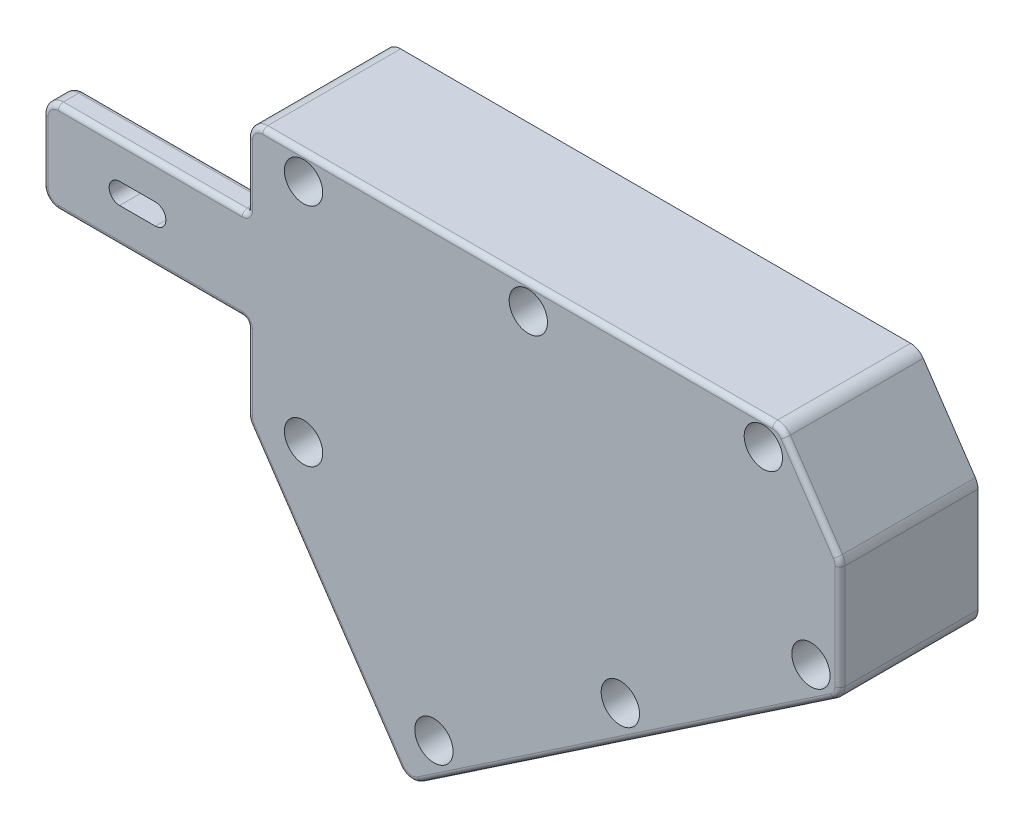
SolidWorks part; units mm, degrees
ref_plane "Front Plane" through (0, 0, 0) normal (0, 0, 1) x (1, 0, 0)
ref_plane "Top Plane" through (0, 0, 0) normal (0, 1, 0) x (1, 0, 0)
ref_plane "Right Plane" through (0, 0, 0) normal (1, 0, 0) x (0, 0, -1)
sketch "Sketch4" plane through (0, 0, -1794.9976) normal (0, 0, 1) x (1, 0, 0)
  line L0 (0.0099, 24.9921) -> (104.4079, 24.9921)
  line L1 (104.4079, 24.9921) -> (116.0099, 7.7914)
  line L2 (116.0099, 7.7914) -> (116.0099, -15.1718)
  line L3 (116.0099, -15.1718) -> (31.3812, -72.2546)
  line L4 (31.3812, -72.2546) -> (0.0099, -25.7448)
  line L5 (0.0099, -25.7448) -> (0.0099, 24.9921)
  circle A0 centre (11.0099, 20) radius 2.25
  circle A1 centre (55, 20) radius 2.25
  circle A2 centre (101.0003, 20.0004) radius 2.25
  circle A3 centre (110.313, -12.2324) radius 2.25
  circle A4 centre (73.0063, -37.396) radius 2.25
  circle A5 centre (36.5275, -62.0013) radius 2.25
  circle A6 centre (11.0099, -24.17) radius 2.25
  dimension "D1" = 4.5
extrude "Boss-Extrude1" add sketch "Sketch4" along normal blind 25
sketch "Sketch5" plane through (0.0099, 0, 0) normal (-1, 0, 0) x (0, 0, 1)
  line L0 (-1794.9976, -111910.8353) -> (-1794.9976, 111863.5728) construction
  circle A0 centre (-1794.9976, 0) radius 15.875
extrude "Cut-Extrude1" cut sketch "Sketch5" against normal up to surface (30 mm away)
sketch "Sketch6" plane through (-11.9282, -8.0457, 0) normal (-0.829, -0.5592, 0) x (0, 0, 1)
  circle A0 centre (-1794.9976, -50.3274) radius 15.875
extrude "Cut-Extrude2" cut sketch "Sketch6" against normal up to surface (35 mm away)
sketch "Sketch7" plane through (30.0099, 0, 0) normal (-1, 0, 0) x (0, 0, 1)
  line L0 (-1794.9976, -111910.8353) -> (-1794.9976, 111863.5728) construction
  circle A0 centre (-1794.9976, 0) radius 14.75
extrude "Cut-Extrude3" cut sketch "Sketch7" against normal blind 3
sketch "Sketch8" plane through (17.0881, 11.5261, 0) normal (-0.829, -0.5592, 0) x (0, 0, 1)
  circle A0 centre (-1794.9976, -50.3274) radius 14.75
extrude "Cut-Extrude4" cut sketch "Sketch8" against normal blind 3
sketch "Sketch9" plane through (0, 0, -1794.9976) normal (0, 0, -1) x (-1, 0, 0)
  line L7 (-33, 15.5) -> (-85.2612, 15.5)
  line L8 (-85.2612, 15.5) -> (-94.5944, 21.7954)
  line L9 (-94.5944, 21.7954) -> (-111.932, -3.903)
  line L10 (-111.932, -3.903) -> (-56.384, -41.3707)
  line L11 (-56.384, -41.3707) -> (-38.934, -15.5)
  line L12 (-38.934, -15.5) -> (-33, -15.5)
  line L13 (-33, -15.5) -> (-33, 15.5)
  line L14 (-33, 15.5) -> (-85.2612, 15.5)
  line L15 (-85.2612, 15.5) -> (-94.5944, 21.7954)
  line L16 (-94.5944, 21.7954) -> (-111.932, -3.903)
  line L17 (-111.932, -3.903) -> (-56.384, -41.3707)
  line L18 (-56.384, -41.3707) -> (-38.934, -15.5)
  line L19 (-38.934, -15.5) -> (-33, -15.5)
  line L20 (-33, -15.5) -> (-33, 15.5)
  dimension "D1" = 0
extrude "Cut-Extrude5" cut sketch "Sketch9" against normal blind 16
sketch "Sketch10" plane through (0, 0, -1778.9976) normal (0, 0, -1) x (-1, 0, 0)
  line L0 (-165897.5145, 111838.5807) -> (165830.1531, -111914.5563) construction
  line L1 (-200090, -0.0079) -> (200022.6386, -0.0079) construction
  circle A0 centre (-89.9882, -0.0079) radius 15.05
extrude "Cut-Extrude6" cut sketch "Sketch10" against normal blind 4
sketch "Sketch11" plane through (0, 0, -1769.9976) normal (0, 0, 1) x (1, 0, 0)
  line L0 (0.0099, 9) -> (-39.9901, 9)
  line L1 (0.0099, 200024.9921) -> (0.0099, -200075.9756) construction
  line L2 (-39.9901, 9) -> (-39.9901, -9)
  line L3 (-39.9901, -9) -> (0.0099, -9)
  line L4 (0.0099, -9) -> (0.0099, 9)
  dimension "D1" = 40
  dimension "D2" = 18
  dimension "D3" = 9
extrude "Boss-Extrude2" add sketch "Sketch11" against normal blind 5
sketch "Sketch12" plane through (0, 0, -1769.9976) normal (0, 0, 1) x (1, 0, 0)
  line L0 (-17.9901, -2.0579) -> (-24.9901, -2.0579) construction
  line L1 (-24.9901, 2.0421) -> (-17.9901, 2.0421) construction
  line L2 (-17.9901, -2.0579) -> (-24.9901, -2.0579)
  line L3 (-24.9901, 2.0421) -> (-17.9901, 2.0421)
  arc A0 (-24.9901, 2.0421) -> (-24.9901, -2.0579) centre (-24.9901, -0.0079) ccw construction
  arc A1 (-17.9901, -2.0579) -> (-17.9901, 2.0421) centre (-17.9901, -0.0079) ccw construction
  arc A2 (-24.9901, 2.0421) -> (-24.9901, -2.0579) centre (-24.9901, -0.0079) ccw
  arc A3 (-17.9901, -2.0579) -> (-17.9901, 2.0421) centre (-17.9901, -0.0079) ccw
extrude "Cut-Extrude7" cut sketch "Sketch12" against normal up to next
fillet "Fillet4" radius 3 6 edges at (31.3812, -72.2546, -1782.4976) (0.0099, -25.7448, -1782.4976) (0.0099, 24.9921, -1782.4976) (104.4079, 24.9921, -1782.4976) (116.0099, 7.7914, -1782.4976) (116.0099, -15.1718, -1782.4976)
fillet "Fillet5" radius 3 2 edges at (-39.9901, 9, -1772.4976) (-39.9901, -9, -1772.4976)
sketch "Sketch14" plane through (0, 0, -1769.9976) normal (0, 0, 1) x (1, 0, 0)
  circle A0 centre (110.313, -12.2324) radius 3.75
  circle A1 centre (73.0063, -37.396) radius 3.75
  circle A2 centre (36.5275, -62.0013) radius 3.75
  circle A3 centre (11.0099, -24.17) radius 3.75
  circle A4 centre (11.0099, 20) radius 3.75
  circle A5 centre (55, 20) radius 3.75
  circle A6 centre (101.0003, 20.0004) radius 3.75
  dimension "D1" = 7.5
extrude "Cut-Extrude8" cut sketch "Sketch14" against normal blind 7.5
fillet "Fillet7" radius 1 8 edges at (0.0099, -9, -1772.4976) (0.0099, 0, -1774.9976) (0.0099, 9, -1772.4976) (-18.4901, 9, -1774.9976) (-39.1114, 8.1213, -1774.9976) (-39.9901, 0, -1774.9976) (-39.1114, -8.1213, -1774.9976) (-18.4901, -9, -1774.9976)
sketch "Sketch15" plane through (0, 0, -1794.9976) normal (0, 0, -1) x (-1, 0, 0)
  line L14 (-8.9953, -35.4896) -> (-7.3373, -36.608)
  line L15 (-2.0099, -15.875) -> (-2.0099, -24.8276)
  line L16 (-2.1809, -25.3868) -> (-8.9953, -35.4896)
  line L17 (-2.0099, -15.875) -> (-2.0099, -24.8276)
  line L18 (-2.1809, -25.3868) -> (-8.9953, -35.4896)
  line L19 (-2.0099, -15.875) -> (-0.0099, -15.875)
  line L20 (-0.0099, -15.875) -> (-0.0099, -24.8276) construction
  line L21 (-0.5228, -26.5052) -> (-7.3373, -36.608) construction
  line L22 (-0.0099, -15.875) -> (-0.0099, -24.8276)
  line L23 (-0.5228, -26.5052) -> (-7.3373, -36.608)
  arc A2 (-0.5228, -26.5052) -> (-0.0099, -24.8276) centre (-3.0099, -24.8276) ccw construction
  arc A3 (-2.1809, -25.3868) -> (-2.0099, -24.8276) centre (-3.0099, -24.8276) ccw
  arc A4 (-2.1809, -25.3868) -> (-2.0099, -24.8276) centre (-3.0099, -24.8276) ccw
  arc A5 (-0.5228, -26.5052) -> (-0.0099, -24.8276) centre (-3.0099, -24.8276) ccw
  dimension "D1" = 2
extrude "Boss-Extrude4" add sketch "Sketch15" along normal blind 2
sketch "Sketch17" plane through (0, 0, -1794.9976) normal (0, 0, -1) x (-1, 0, 0)
  line L0 (-25.0916, -62.9299) -> (-29.7036, -69.7675) construction
  line L1 (-33.8683, -70.577) -> (-114.6875, -16.0638) construction
  line L2 (-116.0099, -13.5767) -> (-116.0099, 6.8742) construction
  line L3 (-115.4971, 8.5518) -> (-105.2999, 23.6697) construction
  line L4 (-0.0099, 21.9921) -> (-0.0099, 15.875) construction
  line L5 (-102.8128, 24.9921) -> (-3.0099, 24.9921) construction
  line L6 (-25.0916, -62.9299) -> (-29.7036, -69.7675)
  line L7 (-33.8683, -70.577) -> (-114.6875, -16.0638)
  line L8 (-116.0099, -13.5767) -> (-116.0099, 6.8742)
  line L9 (-115.4971, 8.5518) -> (-105.2999, 23.6697)
  line L10 (-0.0099, 21.9921) -> (-0.0099, 15.875)
  line L11 (-102.8128, 24.9921) -> (-3.0099, 24.9921)
  line L43 (-26.7497, -61.8116) -> (-25.0916, -62.9299)
  line L44 (-0.0099, 15.875) -> (-2.0099, 15.875)
  line L49 (-2.0099, 21.9921) -> (-2.0099, 15.875)
  line L50 (-26.7497, -61.8116) -> (-31.3617, -68.6491)
  line L51 (-32.7499, -68.919) -> (-113.5691, -14.4057)
  line L52 (-114.0099, -13.5767) -> (-114.0099, 6.8742)
  line L53 (-113.839, 7.4334) -> (-103.6418, 22.5513)
  line L54 (-102.8128, 22.9921) -> (-3.0099, 22.9921)
  line L55 (-2.0099, 21.9921) -> (-2.0099, 15.875)
  line L56 (-26.7497, -61.8116) -> (-31.3617, -68.6491)
  line L57 (-32.7499, -68.919) -> (-113.5691, -14.4057)
  line L58 (-114.0099, -13.5767) -> (-114.0099, 6.8742)
  line L59 (-113.839, 7.4334) -> (-103.6418, 22.5513)
  line L60 (-102.8128, 22.9921) -> (-3.0099, 22.9921)
  arc A0 (-33.8683, -70.577) -> (-29.7036, -69.7675) centre (-32.1907, -68.0899) ccw construction
  arc A1 (-116.0099, -13.5767) -> (-114.6875, -16.0638) centre (-113.0099, -13.5767) ccw construction
  arc A2 (-115.4971, 8.5518) -> (-116.0099, 6.8742) centre (-113.0099, 6.8742) ccw construction
  arc A3 (-102.8128, 24.9921) -> (-105.2999, 23.6697) centre (-102.8128, 21.9921) ccw construction
  arc A4 (-0.0099, 21.9921) -> (-3.0099, 24.9921) centre (-3.0099, 21.9921) ccw construction
  arc A5 (-33.8683, -70.577) -> (-29.7036, -69.7675) centre (-32.1907, -68.0899) ccw
  arc A6 (-116.0099, -13.5767) -> (-114.6875, -16.0638) centre (-113.0099, -13.5767) ccw
  arc A7 (-115.4971, 8.5518) -> (-116.0099, 6.8742) centre (-113.0099, 6.8742) ccw
  arc A8 (-102.8128, 24.9921) -> (-105.2999, 23.6697) centre (-102.8128, 21.9921) ccw
  arc A9 (-0.0099, 21.9921) -> (-3.0099, 24.9921) centre (-3.0099, 21.9921) ccw
  arc A34 (-2.0099, 21.9921) -> (-3.0099, 22.9921) centre (-3.0099, 21.9921) ccw
  arc A35 (-32.7499, -68.919) -> (-31.3617, -68.6491) centre (-32.1907, -68.0899) ccw
  arc A36 (-114.0099, -13.5767) -> (-113.5691, -14.4057) centre (-113.0099, -13.5767) ccw
  arc A37 (-113.839, 7.4334) -> (-114.0099, 6.8742) centre (-113.0099, 6.8742) ccw
  arc A38 (-102.8128, 22.9921) -> (-103.6418, 22.5513) centre (-102.8128, 21.9921) ccw
  arc A39 (-2.0099, 21.9921) -> (-3.0099, 22.9921) centre (-3.0099, 21.9921) ccw
  arc A40 (-32.7499, -68.919) -> (-31.3617, -68.6491) centre (-32.1907, -68.0899) ccw
  arc A41 (-114.0099, -13.5767) -> (-113.5691, -14.4057) centre (-113.0099, -13.5767) ccw
  arc A42 (-113.839, 7.4334) -> (-114.0099, 6.8742) centre (-113.0099, 6.8742) ccw
  arc A43 (-102.8128, 22.9921) -> (-103.6418, 22.5513) centre (-102.8128, 21.9921) ccw
  dimension "D1" = 2
extrude "Boss-Extrude5" add sketch "Sketch17" along normal blind 2
sketch "Sketch20" plane through (-11.9282, -8.0457, 0) normal (-0.829, -0.5592, 0) x (0, 0, 1)
  line L0 (-1794.9976, -34.8273) -> (-1794.9976, -65.8274) construction
  line L1 (-1796.9976, -32.5646) -> (-1796.9976, -34.5788)
  line L2 (-1796.9976, -34.4524) -> (-1796.9976, -22.2661) construction
  line L3 (-1796.9976, -74.4499) -> (-1796.9976, -66.2024) construction
  line L4 (-1796.9976, -66.0759) -> (-1796.9976, -68.0901)
  arc A0 (-1796.9976, -66.0759) -> (-1796.9976, -34.5788) centre (-1794.9976, -50.3273) ccw
  arc A2 (-1796.9976, -68.0901) -> (-1796.9976, -32.5646) centre (-1794.9976, -50.3273) ccw
  circle A4 centre (-1794.9976, -50.3273) radius 15.875 construction
  circle A5 centre (-1794.9976, -50.3273) radius 17.875 construction
  point P1 (-1467.2658, -50.3273)
  point P14 (-1469.9594, -45.6859)
  dimension "D1" = 2
extrude "Boss-Extrude6" add sketch "Sketch20" against normal blind 2
sketch "Sketch21" plane through (0.0099, 0, 0) normal (-1, 0, 0) x (0, 0, 1)
  line L0 (-1796.9976, 16.9334) -> (-1796.9976, 15.7485)
  line L1 (-1796.9976, 15.875) -> (-1796.9976, 21.9921) construction
  line L2 (-1796.9976, -24.8276) -> (-1796.9976, -15.875) construction
  line L3 (-1796.9976, -15.7485) -> (-1796.9976, -16.9334)
  arc A0 (-1796.9976, -15.7485) -> (-1796.9976, 15.7485) centre (-1794.9976, 0) ccw
  arc A1 (-1796.9976, -16.9334) -> (-1796.9976, 16.9334) centre (-1794.9976, 0) ccw
extrude "Boss-Extrude7" add sketch "Sketch21" against normal blind 2
fillet "Fillet8" radius 1 20 edges at (0.141, -25.7047, -1769.9976) (0.0099, -17.4138, -1769.9976) (-0.283, -9.2929, -1769.9976) (-18.9901, -9, -1769.9976) (-39.1114, -8.1213, -1769.9976) (-39.9901, 0, -1769.9976) (-39.1114, 8.1213, -1769.9976) (-18.9901, 9, -1769.9976) (-0.283, 9.2929, -1769.9976) (0.0099, 15.9961, -1769.9976) (0.8886, 24.1134, -1769.9976) (52.9114, 24.9921, -1769.9976) (104.2212, 24.6409, -1769.9976) (110.3985, 16.1107, -1769.9976) (115.8789, 7.7513, -1769.9976) (116.0099, -3.3512, -1769.9976) (115.6588, -14.9851, -1769.9976) (74.2779, -43.3204, -1769.9976) (31.6183, -71.0348, -1769.9976) (15.1132, -48.1363, -1769.9976)
